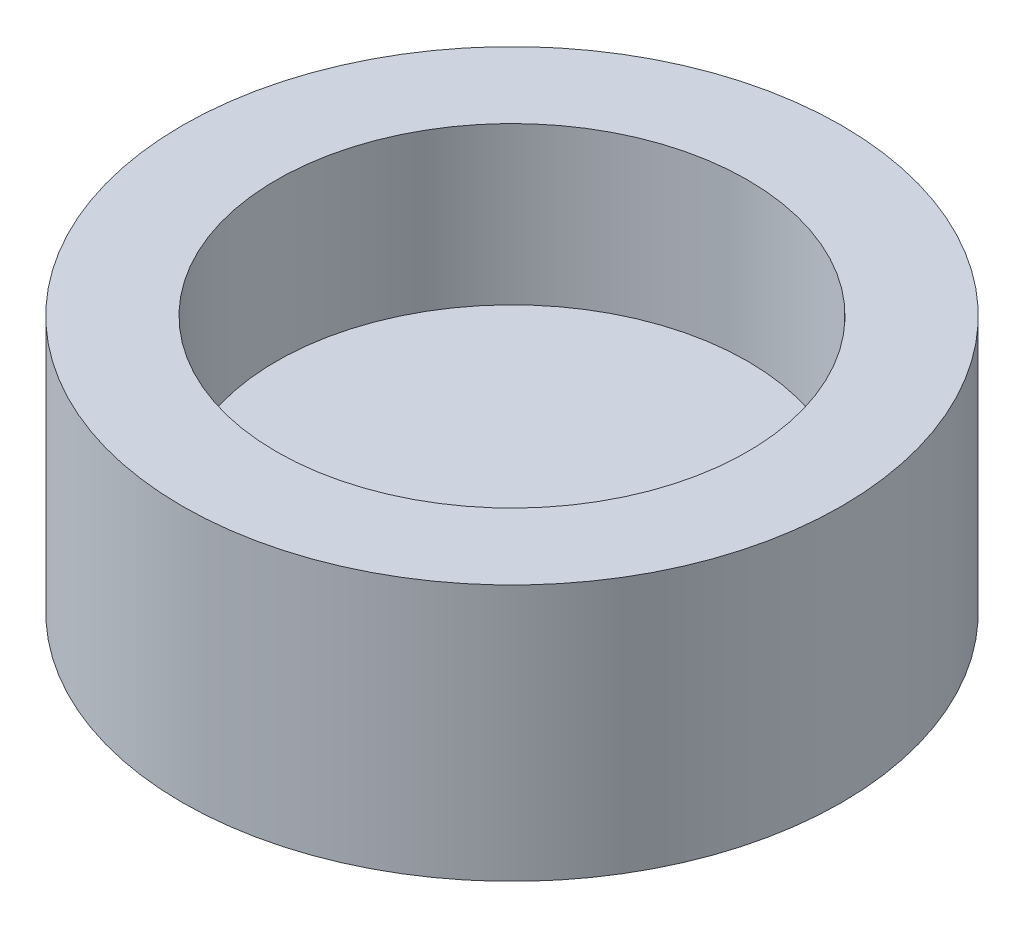
SolidWorks part; units mm, degrees
ref_plane "Front Plane" through (0, 0, 0) normal (0, 0, 1) x (1, 0, 0)
ref_plane "Top Plane" through (0, 0, 0) normal (0, 1, 0) x (1, 0, 0)
ref_plane "Right Plane" through (0, 0, 0) normal (1, 0, 0) x (0, 0, -1)
sketch "Sketch1" plane through (0, 0, 0) normal (0, 1, 0) x (1, 0, 0)
  circle A0 centre (0, 0) radius 10.5
extrude "Boss-Extrude1" add sketch "Sketch1" along normal blind 8.1741
sketch "Sketch2" plane through (0, 0, 0) normal (1, 0, 0) x (0, 0, -1)
  line L0 (0, 8.1741) -> (7.5, 8.1741)
  line L1 (7.5, 3.1741) -> (7.5, 8.1741)
  line L3 (0, 8.1741) -> (0, 3.1741)
  line L4 (-3.4624, 3.1741) -> (-16.0416, 3.1741) construction
  line L5 (7.5, 3.1741) -> (0, 3.1741)
  dimension "D1" = 7.5
  dimension "D2" = 8.1741
  dimension "D3" = 5
sketch "Sketch3" plane through (0, 0, 0) normal (0, 0, 1) x (1, 0, 0)
  line L0 (0, 0.0491) -> (0, 9.5041) construction
revolve "Cut-Revolve2" cut sketch "Sketch2" angle 360 about L0
equation "\"radius\"= 7.5 / 1000"
equation "\"D1@Sketch1\"=\"radius\"*2+.006"
equation "\"a\"= - 32.3127"
equation "\"b\"= .15"
equation "\"c\"=0.005"
equation "\"D1@Boss-Extrude1\" = \"depth\""
equation "\"D2@Sketch2\"=\"depth\""
equation "\"critical\"= - \"b\" / 2 / \"a\""
equation "\"critical_height\"= \"c\" + \"b\" * \"critical\" + \"a\" * \"critical\" ^ 2"
equation "\"center_height\"= \"c\""
equation "\"left_height\"= \"c\" + \"b\" * \"radius\" + \"a\" * \"radius\" ^ 2"
equation "\"max_height\"= \"critical_height\""
equation "\"min_height\"= \"center_height\""
equation "\"depth\"= 0.003 + \"c\" + \"max_height\" - \"min_height\""
